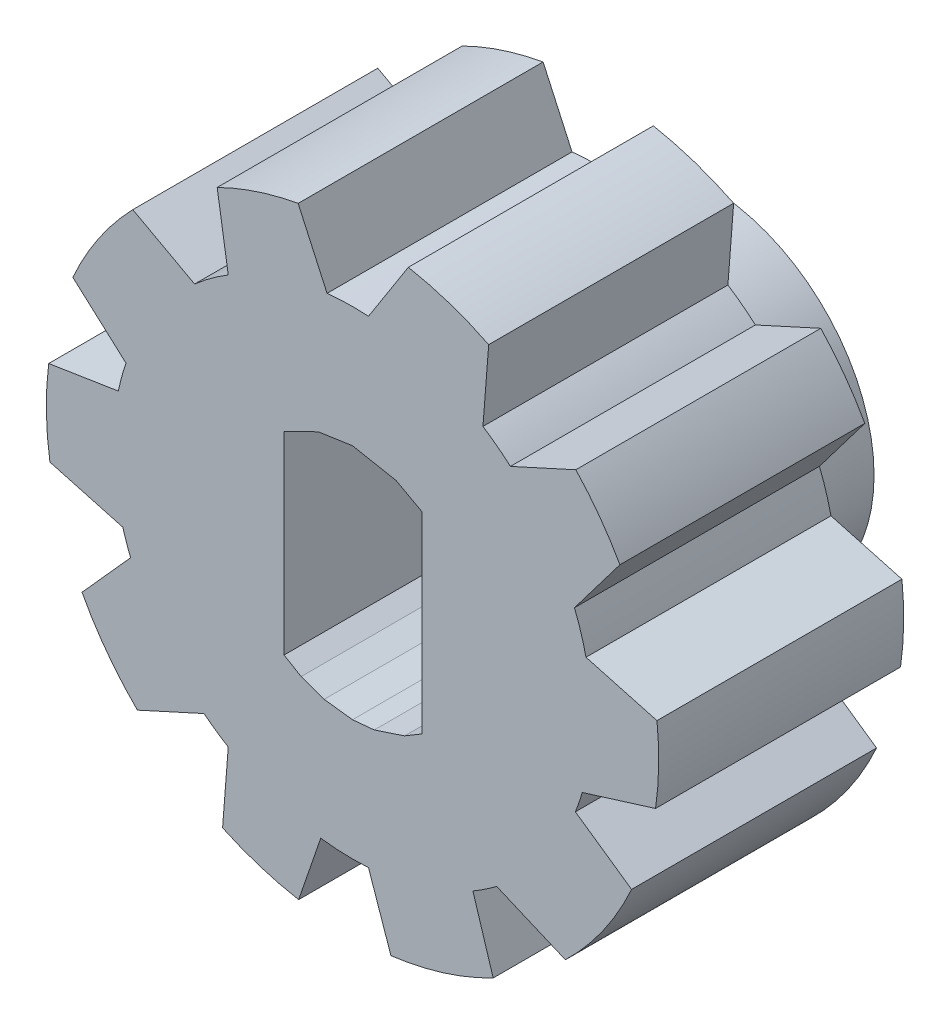
SolidWorks part; units mm, degrees
ref_plane "Front Plane" through (0, 0, 0) normal (0, 0, 1) x (1, 0, 0)
ref_plane "Top Plane" through (0, 0, 0) normal (0, 1, 0) x (1, 0, 0)
ref_plane "Right Plane" through (0, 0, 0) normal (1, 0, 0) x (0, 0, -1)
sketch "Sketch1" plane through (0, 0, 0) normal (0, 0, 1) x (1, 0, 0)
  circle A0 centre (0, 0) radius 6.35
extrude "Boss-Extrude1" add sketch "Sketch1" along normal blind 5.08 contours A0
sketch "Sketch2" plane through (0, 0, 5.08) normal (0, 0, 1) x (1, 0, 0)
  circle A0 centre (0, 0) radius 0.8047
extrude "Cut-Extrude1" cut sketch "Sketch2" against normal blind 5.08
sketch "Sketch6" plane through (0, 0, 0) normal (0, 0, -1) x (-1, 0, 0)
  line L0 (0, 0) -> (-7.1881, 0)
  line L1 (0, 0) -> (-5.6415, -4.0988)
  line L2 (0, 0) -> (-2.1223, -6.5317)
  line L3 (0, 0) -> (2.0812, -6.4054)
  line L4 (0, 0) -> (5.6069, -4.0736)
  line L5 (0, 0) -> (7.3519, 0)
  line L6 (0, 0) -> (-5.9401, 4.3157)
  line L7 (0, 0) -> (-2.1569, 6.6383)
  line L8 (0, 0) -> (2.1034, 6.4737)
  line L9 (0, 0) -> (6.4289, 4.6709)
  line L10 (-6.6219, 0) -> (-6.6219, 0.5964)
  line L11 (-6.6219, 0.5964) -> (-4.8417, 1.0826)
  line L12 (-4.8417, 1.0826) -> (-4.6025, 1.8523)
  line L13 (-4.6025, 1.8523) -> (-5.9401, 3.6164)
  line L14 (-5.9401, 3.6164) -> (-5.0951, 4.556)
  line L15 (-5.0951, 4.556) -> (-3.2749, 3.7269)
  line L16 (-3.2749, 3.7269) -> (-2.7046, 4.1593)
  line L17 (-2.7046, 4.1593) -> (-2.8636, 6.2003)
  line L18 (-2.8636, 6.2003) -> (-1.3873, 6.6035)
  line L19 (-1.3873, 6.6035) -> (-0.3306, 4.9502)
  line L20 (-0.3306, 4.9502) -> (0.5282, 4.9331)
  line L21 (0.5282, 4.9331) -> (1.2891, 6.6035)
  line L22 (1.2891, 6.6035) -> (2.8719, 6.1116)
  line L23 (2.8719, 6.1116) -> (2.5774, 4.2393)
  line L24 (2.5774, 4.2393) -> (3.2749, 3.7269)
  line L25 (3.2749, 3.7269) -> (4.804, 4.556)
  line L26 (4.804, 4.556) -> (5.9683, 2.7344)
  line L27 (5.9683, 2.7344) -> (4.6977, 1.5954)
  line L28 (4.6977, 1.5954) -> (4.8566, 1.014)
  line L29 (4.8566, 1.014) -> (6.6123, 0.7378)
  line L30 (6.6123, 0.7378) -> (6.6123, -0.8801)
  line L31 (6.6123, -0.8801) -> (4.7641, -1.3849)
  line L32 (4.7641, -1.3849) -> (4.6025, -1.8523)
  line L33 (4.6025, -1.8523) -> (5.9683, -3.3759)
  line L34 (5.9683, -3.3759) -> (4.9613, -4.7466)
  line L35 (4.9613, -4.7466) -> (3.0798, -3.8896)
  line L36 (3.0798, -3.8896) -> (2.5774, -4.2393)
  line L37 (2.5774, -4.2393) -> (2.7133, -5.9841)
  line L38 (2.7133, -5.9841) -> (1.1708, -6.4054)
  line L39 (1.1708, -6.4054) -> (0.659, -4.9173)
  line L40 (0.659, -4.9173) -> (-0.3306, -4.9502)
  line L41 (-0.3306, -4.9502) -> (-0.8772, -6.5317)
  line L42 (-0.8772, -6.5317) -> (-2.9897, -5.8752)
  line L43 (-2.9897, -5.8752) -> (-2.4963, -4.2875)
  line L44 (-2.4963, -4.2875) -> (-2.9897, -3.9593)
  line L45 (-2.9897, -3.9593) -> (-4.8417, -4.7466)
  line L46 (-4.8417, -4.7466) -> (-5.9401, -2.7208)
  line L47 (-5.9401, -2.7208) -> (-4.6219, -1.8034)
  line L48 (-4.6219, -1.8034) -> (-4.7641, -1.3849)
  line L49 (-4.7641, -1.3849) -> (-6.6219, -0.8076)
  line L50 (-6.6219, -0.8076) -> (-6.6219, 0)
  circle A0 centre (0, 0) radius 4.9613
  circle A1 centre (0, 0) radius 8.3918
extrude "Cut-Extrude4" cut sketch "Sketch6" against normal blind 5.08
sketch "Sketch7" plane through (0, 0, 0) normal (0, 0, -1) x (-1, 0, 0)
  circle A0 centre (0, 0) radius 3.4769
extrude "Boss-Extrude3" add sketch "Sketch7" along normal blind 2.2586
sketch "Sketch10" plane through (0, 0, 5.08) normal (0, 0, 1) x (1, 0, 0)
  line L0 (0, 0) -> (1.4372, 0)
  line L1 (0, 0) -> (-1.4205, 0)
  line L2 (-1.4205, 0) -> (-1.4205, 2.0087)
  line L3 (-1.4205, 2.0087) -> (-0.7103, 2.3555)
  line L4 (-0.7103, 2.3555) -> (0, 2.4602)
  line L5 (0, 2.4602) -> (0.9023, 2.2888)
  line L6 (0.9023, 2.2888) -> (1.4372, 1.9968)
  line L7 (1.4372, 1.9968) -> (1.4372, 0)
  line L8 (1.4372, -1.9968) -> (1.0794, -2.2108)
  line L9 (1.0794, -2.2108) -> (0.4511, -2.4185)
  line L10 (0.4511, -2.4185) -> (0, -2.4602)
  line L11 (0, -2.4602) -> (-0.5887, -2.3888)
  line L12 (-0.5887, -2.3888) -> (-1.0654, -2.2176)
  line L13 (-1.0654, -2.2176) -> (-1.4205, -2.0087)
  line L14 (-1.4205, -2.0087) -> (-1.4205, 0)
  line L15 (-1.4205, 2.0087) -> (-0.7103, 2.3555)
  line L16 (0, 2.4602) -> (0.9023, 2.2888)
  line L17 (1.4372, 1.9968) -> (1.4372, 0)
  line L18 (1.4372, 0) -> (1.4372, -1.9968)
  circle A0 centre (0, 0) radius 2.4602
  circle M42 centre (0, 0) radius 0.8047
extrude "Cut-Extrude5" cut sketch "Sketch10" against normal blind 5.1226 contours L18 L0 L1 L14 L13 L12 L11 L10 L9 L8 M42 | L0 L1 M42 | L1 L0 M42 | L7 L6 L5 L4 L3 L2 L1 L0 M42
sketch "Sketch11" plane through (0, 0, -2.2586) normal (0, 0, -1) x (-1, 0, 0)
  circle A0 centre (0, 0) radius 0.4748
extrude "Cut-Extrude6" cut sketch "Sketch11" against normal blind 9.144
